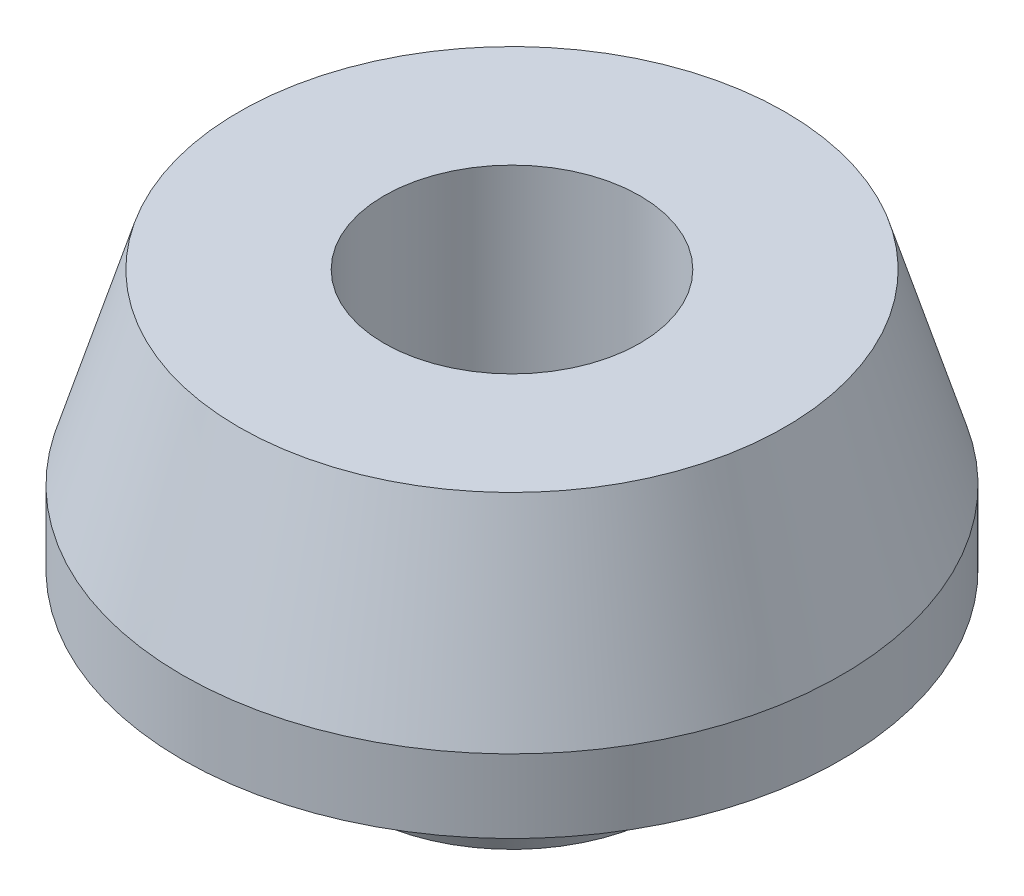
SolidWorks part; units mm, degrees
ref_plane "Front Plane" through (0, 0, 0) normal (0, 0, 1) x (1, 0, 0)
ref_plane "Top Plane" through (0, 0, 0) normal (0, 1, 0) x (1, 0, 0)
ref_plane "Right Plane" through (0, 0, 0) normal (1, 0, 0) x (0, 0, -1)
sketch "Sketch1" plane through (0, 0, 0) normal (0, 0, 1) x (1, 0, 0)
  line L0 (4.8, 0) -> (5.8, 0)
  line L1 (5.8, 0) -> (7.6199, 5)
  line L2 (7.6199, 5) -> (12.3699, 5)
  line L3 (12.3699, 5) -> (12.3699, 7.75)
  line L4 (12.3699, 7.75) -> (10.25, 14.75)
  line L5 (10.25, 14.75) -> (4.8, 14.75)
  line L6 (4.8, 14.75) -> (4.8, 0)
  line L7 (0, 0) -> (0, 17.8051) construction
  dimension "D1" = 14.75
  dimension "D2" = 4.8
  dimension "D3" = 2.75
  dimension "D4" = 9.75
  dimension "D5" = 4.75
  dimension "D6" = 110
  dimension "D7" = 5.45
  dimension "D8" = 1
revolve "Revolve1" add sketch "Sketch1" angle 360 about L7
